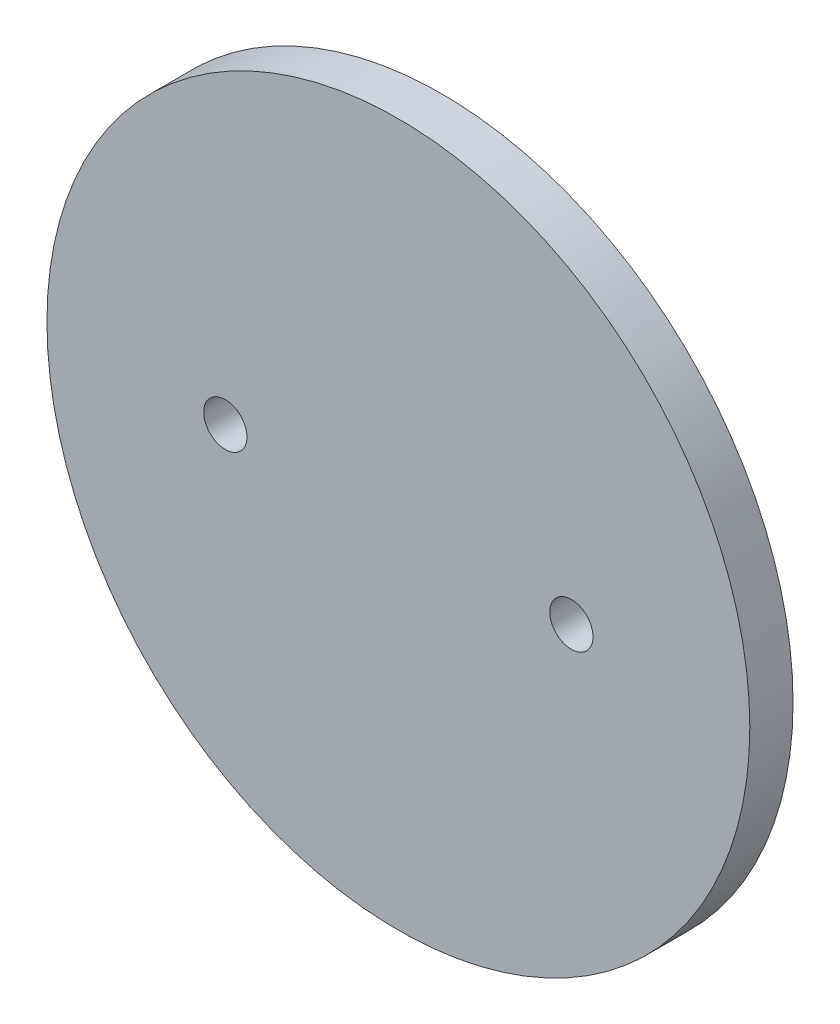
SolidWorks part; units mm, degrees
ref_plane "Front Plane" through (0, 0, 0) normal (0, 0, 1) x (1, 0, 0)
ref_plane "Top Plane" through (0, 0, 0) normal (0, 1, 0) x (1, 0, 0)
ref_plane "Right Plane" through (0, 0, 0) normal (1, 0, 0) x (0, 0, -1)
sketch "Sketch1" plane through (0, 0, 0) normal (0, 0, 1) x (1, 0, 0)
  circle A0 centre (0, 0) radius 20.6375
extrude "Boss-Extrude1" add sketch "Sketch1" along normal blind 2.54
sketch "Sketch2" plane through (0, 0, 2.54) normal (0, 0, 1) x (1, 0, 0)
  line L0 (-20.6375, 0) -> (20.6375, 0)
  circle A0 centre (0, 0) radius 20.6375 construction
  circle A1 centre (-10.16, 0) radius 1.27
  circle A2 centre (10.16, 0) radius 1.27
  point P7 (0, 0)
  dimension "D1" = 10.16
  dimension "D2" = 10.16
extrude "Cut-Extrude1" cut sketch "Sketch2" against normal through all contours L0 A1 | L0 A1 | L0 A2 | L0 A2
